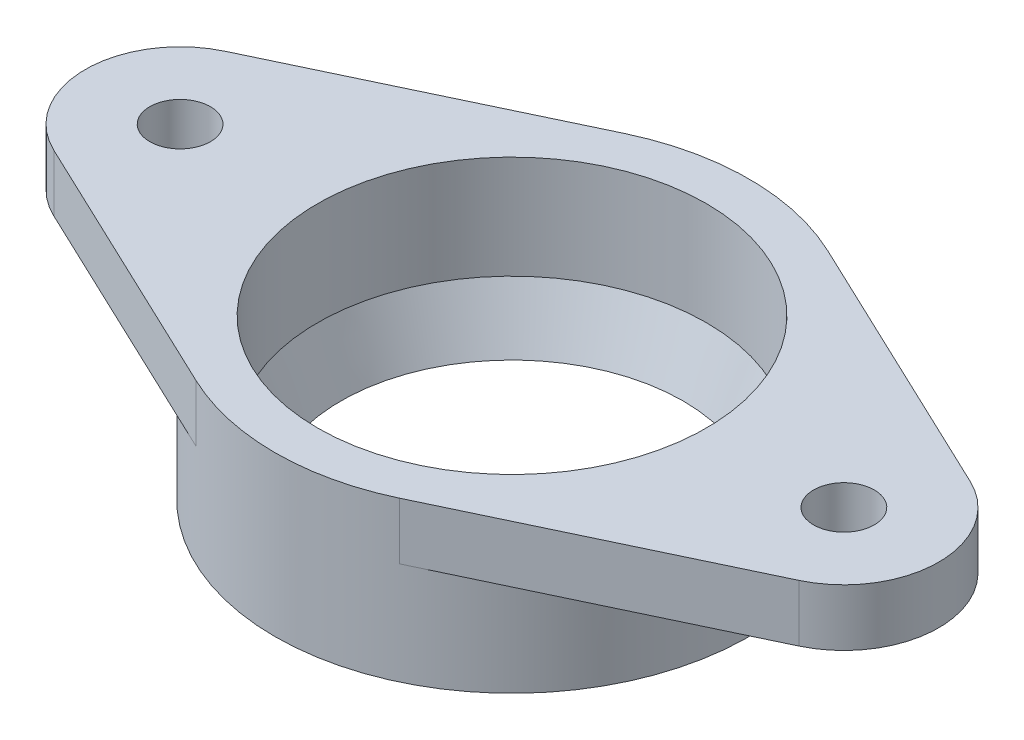
SolidWorks part; units mm, degrees
ref_plane "Front Plane" through (0, 0, 0) normal (0, 0, 1) x (1, 0, 0)
ref_plane "Top Plane" through (0, 0, 0) normal (0, 1, 0) x (1, 0, 0)
ref_plane "Right Plane" through (0, 0, 0) normal (1, 0, 0) x (0, 0, -1)
sketch "Sketch1" plane through (0, 0, 0) normal (0, 1, 0) x (1, 0, 0)
  circle A0 centre (0, 0) radius 12.5
  dimension "D1" = 25
extrude "Boss-Extrude1" add sketch "Sketch1" against normal blind 8.4
sketch "Sketch2" plane through (0, -8.4, 0) normal (0, -1, 0) x (1, 0, 0)
  circle A0 centre (0, 0) radius 10.25
  dimension "D1" = 20.5
extrude "Cut-Extrude1" cut sketch "Sketch2" against normal through all both and the other way through all
sketch "Sketch3" plane through (0, 0, 0) normal (1, 0, 0) x (0, 0, -1)
  line L0 (0, 4.62) -> (0, -4.62) construction
  line L1 (-12.5, -8.4) -> (12.5, -8.4) construction
  line L2 (9.0239, -8.4) -> (12.5, 0)
  line L3 (12.5, -8.4) -> (12.5, 0) construction
  line L4 (12.5, 0) -> (12.5, -8.4)
  line L5 (12.5, -8.4) -> (9.0239, -8.4)
  line L6 (12.5, 0) -> (-12.5, 0) construction
  circle A0 centre (0, -3.4) radius 10.25 construction
  point P8 (12.5, 0)
  dimension "D1" = 20.5
  dimension "D2" = 5
ref_axis "Axis1" through (0, -24.717, 0) along (0, 1, 0)
revolve "Revolve1" add sketch "Sketch3" angle 360 about axis through (0, -24.717, 0) along (0, 1, 0)
sketch "Sketch4" plane through (0, 0, 0) normal (0, 1, 0) x (1, 0, 0)
  line L0 (-5.3571, 11.2938) -> (-19.6429, 4.5175)
  line L1 (-31.5087, 0) -> (29.0808, 0) construction
  line L2 (-12.5, 0) -> (-12.5, -6.5741) construction
  line L3 (-4.62, 0) -> (4.62, 0) construction
  line L5 (-5.3571, -11.2938) -> (-19.6429, -4.5175)
  line L6 (0, -4.62) -> (0, 4.62) construction
  line L7 (5.3571, -11.2938) -> (19.6429, -4.5175)
  line L8 (5.3571, 11.2938) -> (19.6429, 4.5175)
  circle A0 centre (0, 0) radius 12.5 construction
  arc A1 (-19.6429, 4.5175) -> (-19.6429, -4.5175) centre (-17.5, 0) ccw
  arc A2 (19.6429, 4.5175) -> (19.6429, -4.5175) centre (17.5, 0) cw
  arc A3 (-5.3571, 11.2938) -> (-5.3571, -11.2938) centre (0, 0) ccw
  arc A4 (5.3571, -11.2938) -> (5.3571, 11.2938) centre (0, 0) ccw
  circle A5 centre (-17.5, 0) radius 1.6
  circle A6 centre (17.5, 0) radius 1.6
  dimension "D1" = 3.2
  dimension "D2" = 5
extrude "Boss-Extrude2" add sketch "Sketch4" against normal blind 3
